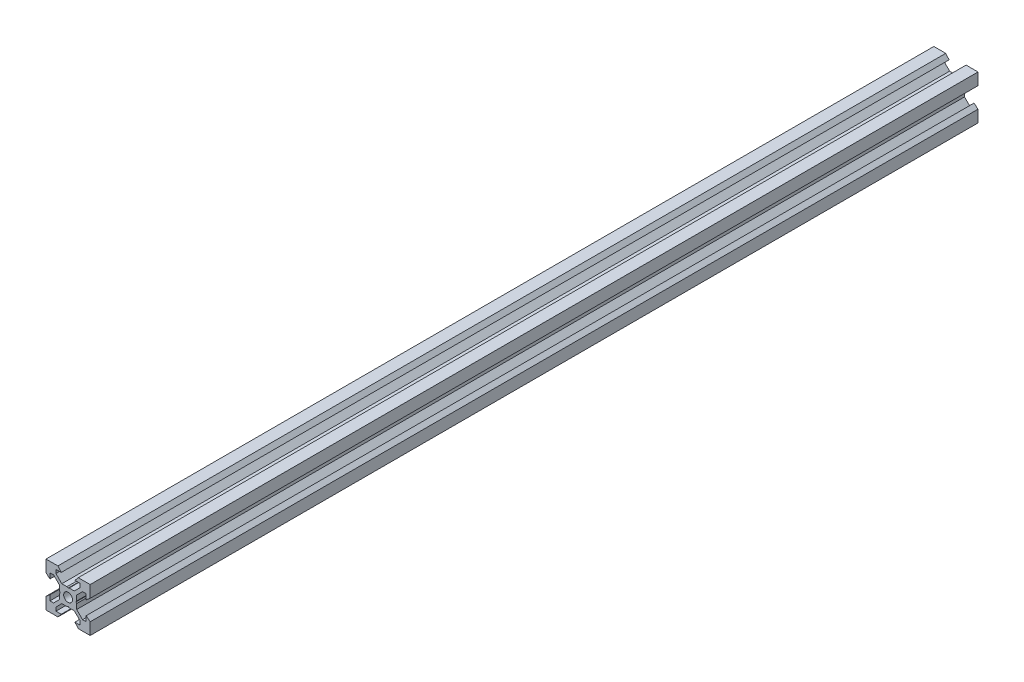
SolidWorks part; units mm, degrees
ref_plane "Front Plane" through (0, 0, 0) normal (0, 0, 1) x (1, 0, 0)
ref_plane "Top Plane" through (0, 0, 0) normal (0, 1, 0) x (1, 0, 0)
ref_plane "Right Plane" through (0, 0, 0) normal (1, 0, 0) x (0, 0, -1)
sketch "Sketch1" plane through (0, 0, 0) normal (0, 0, 1) x (1, 0, 0)
  line L0 (10, 10) -> (4.6104, 10) construction
  line L1 (10, 10) -> (10, 4.6104) construction
  line L2 (10, -10) -> (10, -4.6104) construction
  line L3 (10, -10) -> (4.6104, -10) construction
  line L4 (10, 10) -> (10, 4.6104)
  line L5 (6.5607, 5.5) -> (8.2, 5.5)
  line L6 (5.5, 8.2) -> (5.5, 6.5607)
  line L7 (10, 10) -> (4.6104, 10)
  line L8 (10, 10) -> (10, 4.6104)
  line L9 (6.5607, 5.5) -> (3.9, 2.8393)
  line L10 (5.5, 6.5607) -> (2.8393, 3.9)
  line L11 (10, 4.6104) -> (8.2, 3.1)
  line L12 (4.6104, 10) -> (3.1, 8.2)
  line L13 (8.2, 3.1) -> (8.2, 5.5)
  line L14 (3.1, 8.2) -> (5.5, 8.2)
  line L15 (-6.5607, 5.5) -> (-8.2, 5.5)
  line L16 (6.5607, -5.5) -> (8.2, -5.5)
  line L17 (3.1, -8.2) -> (5.5, -8.2)
  line L18 (8.2, -3.1) -> (8.2, -5.5)
  line L19 (4.6104, -10) -> (3.1, -8.2)
  line L20 (10, -4.6104) -> (8.2, -3.1)
  line L21 (0.5196, -3.9) -> (0, -3.6)
  line L22 (0.5196, 3.9) -> (0, 3.6)
  line L23 (3.6, 0) -> (3.9, -0.5196)
  line L24 (3.9, 0.5196) -> (3.6, 0)
  line L25 (3.9, 0.5196) -> (3.9, 2.8393)
  line L26 (2.8393, 3.9) -> (0.5196, 3.9)
  line L27 (3.9, -2.8393) -> (3.9, -0.5196)
  line L28 (2.8393, -3.9) -> (0.5196, -3.9)
  line L29 (5.5, -6.5607) -> (2.8393, -3.9)
  line L30 (6.5607, -5.5) -> (3.9, -2.8393)
  line L31 (10, -10) -> (10, -4.6104)
  line L32 (10, -10) -> (4.6104, -10)
  line L33 (5.5, -8.2) -> (5.5, -6.5607)
  line L34 (-6.5607, -5.5) -> (-8.2, -5.5)
  line L35 (10, -10) -> (10, -4.6104)
  line L36 (0, 0) -> (0, 8.2) construction
  line L37 (-10, -10) -> (-4.6104, -10) construction
  line L38 (-10, -10) -> (-10, -4.6104) construction
  line L39 (-10, 10) -> (-10, 4.6104) construction
  line L40 (-10, 10) -> (-4.6104, 10) construction
  line L41 (-10, -10) -> (-10, -4.6104)
  line L43 (-5.5, -8.2) -> (-5.5, -6.5607)
  line L44 (-10, -10) -> (-4.6104, -10)
  line L45 (-10, -10) -> (-10, -4.6104)
  line L46 (-6.5607, -5.5) -> (-3.9, -2.8393)
  line L47 (-5.5, -6.5607) -> (-2.8393, -3.9)
  line L48 (-2.8393, -3.9) -> (-0.5196, -3.9)
  line L49 (-3.9, -2.8393) -> (-3.9, -0.5196)
  line L50 (-2.8393, 3.9) -> (-0.5196, 3.9)
  line L51 (-3.9, 0.5196) -> (-3.9, 2.8393)
  line L52 (-3.9, 0.5196) -> (-3.6, 0)
  line L53 (-3.6, 0) -> (-3.9, -0.5196)
  line L54 (-0.5196, 3.9) -> (0, 3.6)
  line L55 (-0.5196, -3.9) -> (0, -3.6)
  line L56 (-10, -4.6104) -> (-8.2, -3.1)
  line L57 (-4.6104, -10) -> (-3.1, -8.2)
  line L58 (-8.2, -3.1) -> (-8.2, -5.5)
  line L59 (-3.1, -8.2) -> (-5.5, -8.2)
  line L60 (-10, -10) -> (10, -10) construction
  line L61 (-10, -10) -> (-10, 10) construction
  line L62 (-3.1, 8.2) -> (-5.5, 8.2)
  line L63 (-8.2, 3.1) -> (-8.2, 5.5)
  line L64 (-4.6104, 10) -> (-3.1, 8.2)
  line L65 (-10, 4.6104) -> (-8.2, 3.1)
  line L66 (-5.5, 6.5607) -> (-2.8393, 3.9)
  line L67 (-6.5607, 5.5) -> (-3.9, 2.8393)
  line L68 (-10, 10) -> (-10, 4.6104)
  line L69 (-10, 10) -> (-4.6104, 10)
  line L70 (-5.5, 8.2) -> (-5.5, 6.5607)
  line L71 (-10, 10) -> (10, 10) construction
  line L72 (-10, 10) -> (-10, 4.6104)
  line L73 (10, -10) -> (10, 10) construction
  line L74 (-10, -10) -> (10, 10) construction
  line L75 (-10, 10) -> (10, -10) construction
  circle A0 centre (0, 0) radius 2
  dimension "D7" = 4
  dimension "D1" = 20
  dimension "D2" = 5.3896
  dimension "D3" = 4.5
  dimension "D4" = 50
  dimension "D5" = 1.8
  dimension "D6" = 1.5104
  dimension "D8" = 5.5
  dimension "D9" = 120
  dimension "D10" = 0.3
  dimension "D11" = 2.3197
  dimension "D12" = 7.8
  dimension "D13" = 7.8
  dimension "D14" = 1.5
  dimension "D15" = 2.6607
extrude "Boss-Extrude1" add sketch "Sketch1" along normal mid plane 402 contours L70 L62 L64 L69 L68 L65 L63 L15 L67 L51 L52 L53 L49 L46 L34 L58 L56 L41 L44 L57 L59 L43 L47 L48 L55 L21 L28 L29 L33 L17 L19 L32 L31 L20 L18 L16 L30 L27 L23 L24 L25 L9 L5 L13 L11 L4 L7 L12 L14 L6 L10
